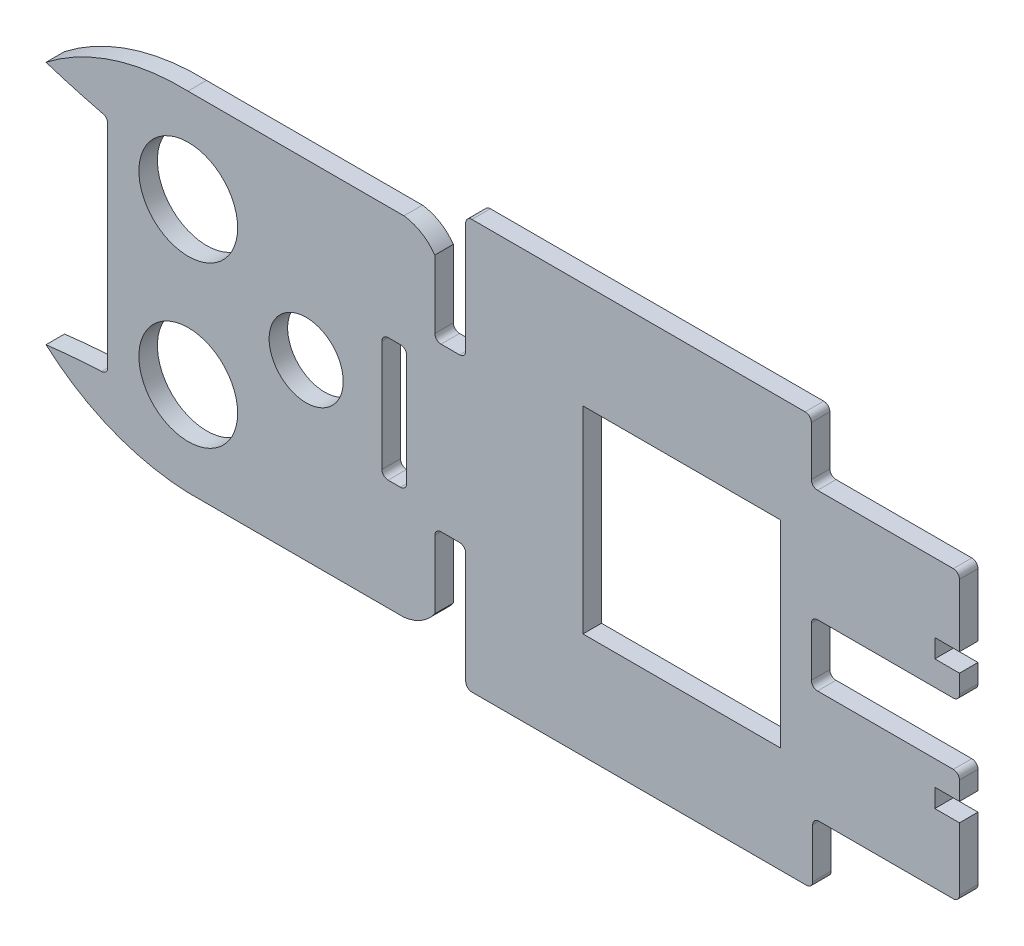
SolidWorks part; units mm, degrees
ref_plane "Alzado" through (0, 0, 0) normal (0, 0, 1) x (1, 0, 0)
ref_plane "Planta" through (0, 0, 0) normal (0, 1, 0) x (1, 0, 0)
ref_plane "Vista lateral" through (0, 0, 0) normal (1, 0, 0) x (0, 0, -1)
sketch "Model" plane through (0, 0, 0) normal (0, 0, 1) x (1, 0, 0)
  line L0 (34.361, 35.5407) -> (34.361, 20.0407)
  line L1 (66.361, 35.5407) -> (34.361, 35.5407)
  line L2 (66.361, 3.5407) -> (66.361, 35.5407)
  line L3 (34.361, 3.5407) -> (66.361, 3.5407)
  line L4 (34.361, 20.0407) -> (34.361, 3.5407)
  line L5 (-29.639, -8.623) -> (5.361, -8.623)
  line L6 (-42.6501, 36.7049) -> (-42.639, 2.377)
  line L7 (4.7904, 29.3389) -> (2.7904, 29.3389)
  line L8 (5.7904, 10.3389) -> (5.7904, 28.3389)
  line L9 (2.7904, 9.3389) -> (4.7904, 9.3389)
  line L10 (1.7904, 28.3389) -> (1.7904, 10.3389)
  line L11 (10.361, 33.7043) -> (10.361, 44.7043)
  line L12 (-29.639, 47.7043) -> (5.361, 47.7043)
  line L13 (10.361, -5.623) -> (10.361, 5.377)
  line L14 (38.2952, -13.6135) -> (70.5828, -13.623)
  line L15 (71.361, 43.7043) -> (71.361, 51.7043)
  line L16 (94.361, 42.7043) -> (72.361, 42.7043)
  line L17 (95.361, 31.5407) -> (95.361, 41.7043)
  line L18 (91.361, 31.5407) -> (95.361, 31.5407)
  line L19 (91.361, 28.5407) -> (91.361, 31.5407)
  line L20 (95.361, 28.5407) -> (91.361, 28.5407)
  line L21 (95.361, 25.5407) -> (95.361, 28.5407)
  line L22 (72.361, 24.5407) -> (94.361, 24.5407)
  line L23 (71.361, 15.5407) -> (71.361, 23.5407)
  line L24 (94.361, 14.5407) -> (72.361, 14.5407)
  line L25 (95.361, 10.5407) -> (95.361, 13.5407)
  line L26 (91.361, 10.5407) -> (95.361, 10.5407)
  line L27 (91.361, 7.5407) -> (91.361, 10.5407)
  line L28 (95.361, 7.5407) -> (91.361, 7.5407)
  line L29 (95.361, -2.623) -> (95.361, 7.5407)
  line L30 (72.5828, -3.623) -> (94.361, -3.623)
  line L31 (71.5828, -12.623) -> (71.5828, -4.623)
  line L32 (16.361, -13.623) -> (38.2952, -13.6135)
  line L33 (45.361, 52.7043) -> (70.361, 52.7043)
  line L34 (16.361, 52.7043) -> (45.361, 52.7043)
  line L35 (14.361, 32.7043) -> (11.361, 32.7043)
  line L36 (15.361, 51.7043) -> (15.361, 33.7043)
  line L37 (15.361, 5.377) -> (15.361, -12.623)
  line L38 (11.361, 6.377) -> (14.361, 6.377)
  arc A0 (-52.639, 0.6222) -> (-29.639, -8.623) centre (-28.2985, 27.944) ccw
  arc A1 (-43.639, 1.377) -> (-52.639, 0.6222) centre (-38.2805, -116.5358) ccw
  arc A2 (-43.639, 1.377) -> (-42.639, 2.377) centre (-43.639, 2.377) ccw
  arc A3 (-42.6501, 36.7049) -> (-43.6501, 37.7049) centre (-43.6501, 36.7049) ccw
  arc A4 (-52.639, 40.2528) -> (-43.6501, 37.7049) centre (-14.8167, 156.5566) ccw
  arc A5 (-29.639, 47.7043) -> (-52.639, 40.2528) centre (-30.7897, 12.0341) ccw
  arc A6 (5.7904, 28.3389) -> (4.7904, 29.3389) centre (4.7904, 28.3389) ccw
  arc A7 (4.7904, 9.3389) -> (5.7904, 10.3389) centre (4.7904, 10.3389) ccw
  arc A8 (1.7904, 10.3389) -> (2.7904, 9.3389) centre (2.7904, 10.3389) ccw
  arc A9 (2.7904, 29.3389) -> (1.7904, 28.3389) centre (2.7904, 28.3389) ccw
  arc A10 (10.361, 44.7043) -> (5.361, 47.7043) centre (4.4692, 40.5513) ccw
  arc A11 (10.361, 33.7043) -> (11.361, 32.7043) centre (11.361, 33.7043) ccw
  arc A12 (11.361, 6.377) -> (10.361, 5.377) centre (11.361, 5.377) ccw
  arc A13 (5.361, -8.623) -> (10.361, -5.623) centre (4.4692, -1.4699) ccw
  arc A14 (71.361, 51.7043) -> (70.361, 52.7043) centre (70.361, 51.7043) ccw
  arc A15 (71.361, 43.7043) -> (72.361, 42.7043) centre (72.361, 43.7043) ccw
  arc A16 (95.361, 41.7043) -> (94.361, 42.7043) centre (94.361, 41.7043) ccw
  arc A17 (94.361, 24.5407) -> (95.361, 25.5407) centre (94.361, 25.5407) ccw
  arc A18 (72.361, 24.5407) -> (71.361, 23.5407) centre (72.361, 23.5407) ccw
  arc A19 (71.361, 15.5407) -> (72.361, 14.5407) centre (72.361, 15.5407) ccw
  arc A20 (95.361, 13.5407) -> (94.361, 14.5407) centre (94.361, 13.5407) ccw
  arc A21 (94.361, -3.623) -> (95.361, -2.623) centre (94.361, -2.623) ccw
  arc A22 (72.5828, -3.623) -> (71.5828, -4.623) centre (72.5828, -4.623) ccw
  arc A23 (70.5828, -13.623) -> (71.5828, -12.623) centre (70.5828, -12.623) ccw
  arc A24 (14.361, 32.7043) -> (15.361, 33.7043) centre (14.361, 33.7043) ccw
  arc A25 (16.361, 52.7043) -> (15.361, 51.7043) centre (16.361, 51.7043) ccw
  arc A26 (15.361, -12.623) -> (16.361, -13.623) centre (16.361, -12.623) ccw
  arc A27 (15.361, 5.377) -> (14.361, 6.377) centre (14.361, 5.377) ccw
  arc A28 (10.361, 33.7043) -> (11.361, 32.7043) centre (11.361, 33.7043) ccw
  arc A29 (11.361, 6.377) -> (10.361, 5.377) centre (11.361, 5.377) ccw
  circle A30 centre (-29.5875, 32.541) radius 8
  circle A31 centre (-10.4865, 19.541) radius 6
  circle A32 centre (-29.5875, 6.541) radius 8
extrude "Saliente-Extruir1" add sketch "Model" along normal blind 3 contours A27 L37 A26 L32 L14 A23 L31 A22 L30 A21 L29 L28 L27 L26 L25 A20 L24 A19 L23 A18 L22 A17 L21 L20 L19 L18 L17 A16 L16 A15 L15 A14 L33 L34 A25 L36 A24 L35 A11 L11 A10 L12 A5 A4 A3 L6 A2 A1 A0 L5 A13
